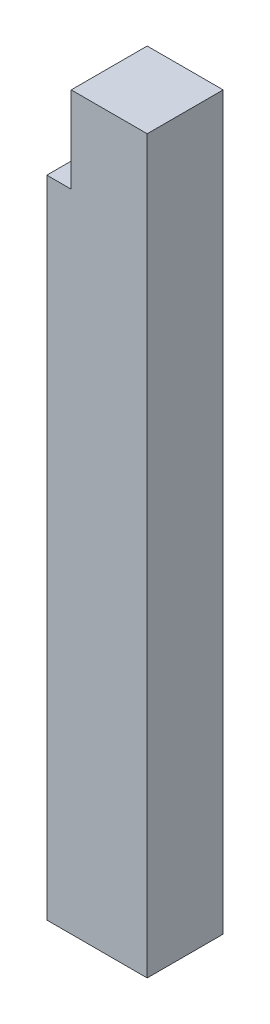
SolidWorks part; units mm, degrees
ref_plane "Front Plane" through (0, 0, 0) normal (0, 0, 1) x (1, 0, 0)
ref_plane "Top Plane" through (0, 0, 0) normal (0, 1, 0) x (1, 0, 0)
ref_plane "Right Plane" through (0, 0, 0) normal (1, 0, 0) x (0, 0, -1)
sketch "Sketch2" plane through (0, 0, 0) normal (0, 1, 0) x (1, 0, 0)
  line L0 (-3.4291, 0.875) -> (-3.4291, 2.7037)
  line L1 (-3.4291, -2.5963) -> (3.5709, -2.5963)
  line L2 (-3.4291, -2.5963) -> (-3.4291, -0.875)
  line L3 (-3.4291, 2.7037) -> (3.5709, 2.7037)
  line L4 (3.5709, -2.5963) -> (3.5709, 2.7037)
  line L5 (-3.4291, -2.5963) -> (-1.1557, -0.875) construction
  line L6 (-3.4291, 2.7037) -> (-1.1098, 0.875) construction
  line L7 (-3.4291, -0.875) -> (0.9596, -0.875)
  line L9 (-3.4291, 0.875) -> (0.9596, 0.875)
  line L10 (0.9596, -0.875) -> (0.9596, 0.875)
  line L13 (0.9596, 0.7266) -> (3.5709, 2.7037) construction
  line L14 (0.9596, -0.4342) -> (3.5709, -2.5963) construction
  point P0 (0, 0)
  point P6 (-3.5404, 0.28)
  dimension "D1" = 7
  dimension "D2" = 5.3
  dimension "D3" = 1.75
  dimension "D4" = 4.5
  dimension "D5" = 0.875
extrude "Boss-Extrude2" add sketch "Sketch2" along normal blind 45
sketch "Sketch3" plane through (0, 45, 0) normal (0, 1, 0) x (1, 0, 0)
  line L0 (-3.4291, -2.5963) -> (3.5709, -2.5963) construction
  line L1 (3.5709, 2.7037) -> (-1.7291, 2.7037)
  line L2 (3.5709, 2.7037) -> (3.5709, -2.5963)
  line L3 (3.5709, -2.5963) -> (-1.7291, -2.5963)
  line L4 (-1.7291, 2.7037) -> (-1.7291, -2.5963)
extrude "Boss-Extrude3" add sketch "Sketch3" along normal blind 6
